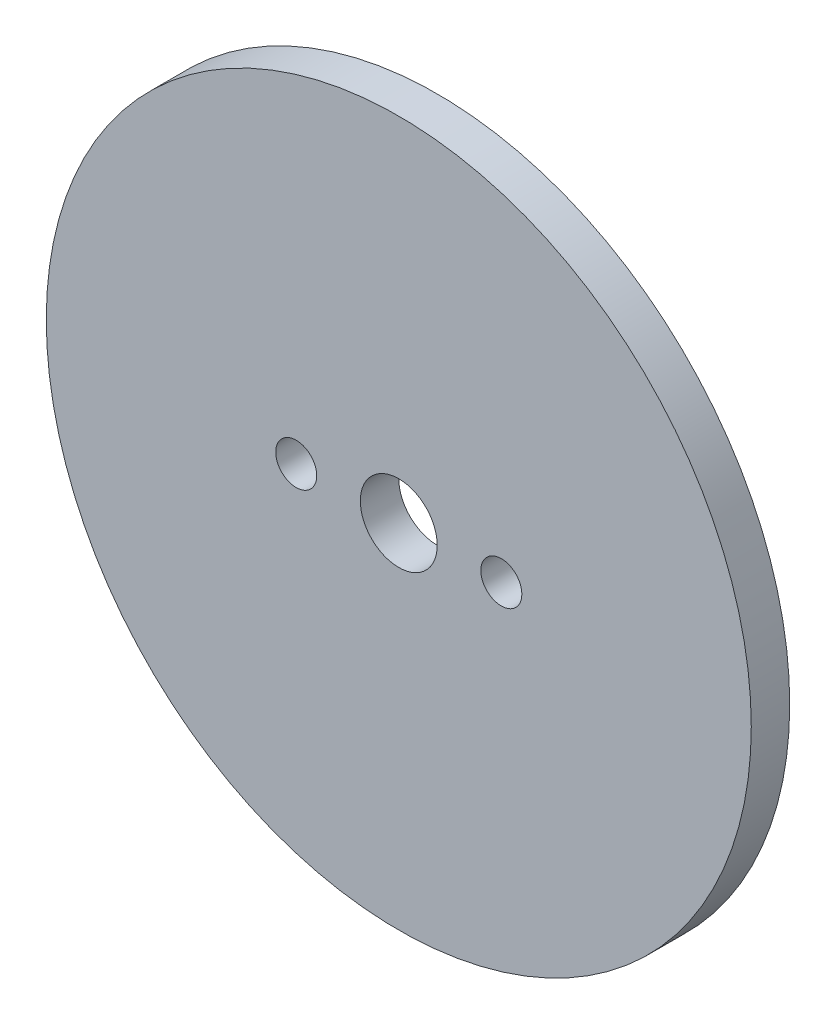
SolidWorks part; units mm, degrees
material "MDF"
ref_plane "Plano frontal" through (0, 0, 0) normal (0, 0, 1) x (1, 0, 0)
ref_plane "Plano superior" through (0, 0, 0) normal (0, 1, 0) x (1, 0, 0)
ref_plane "Plano direito" through (0, 0, 0) normal (1, 0, 0) x (0, 0, -1)
sketch "Esboço1" plane through (0, 0, 0) normal (0, 0, 1) x (1, 0, 0)
  line L0 (-8, 0) -> (8, 0) construction
  circle A0 centre (0, 0) radius 27.5
  circle A1 centre (0, 0) radius 3
  circle A2 centre (-8, 0) radius 1.6
  circle A3 centre (8, 0) radius 1.6
  dimension "D1" = 3.2
  dimension "D2" = 6
  dimension "D4" = 55
  dimension "D3" = 16
extrude "Ressalto-extrusão1" add sketch "Esboço1" along normal mid plane 3
